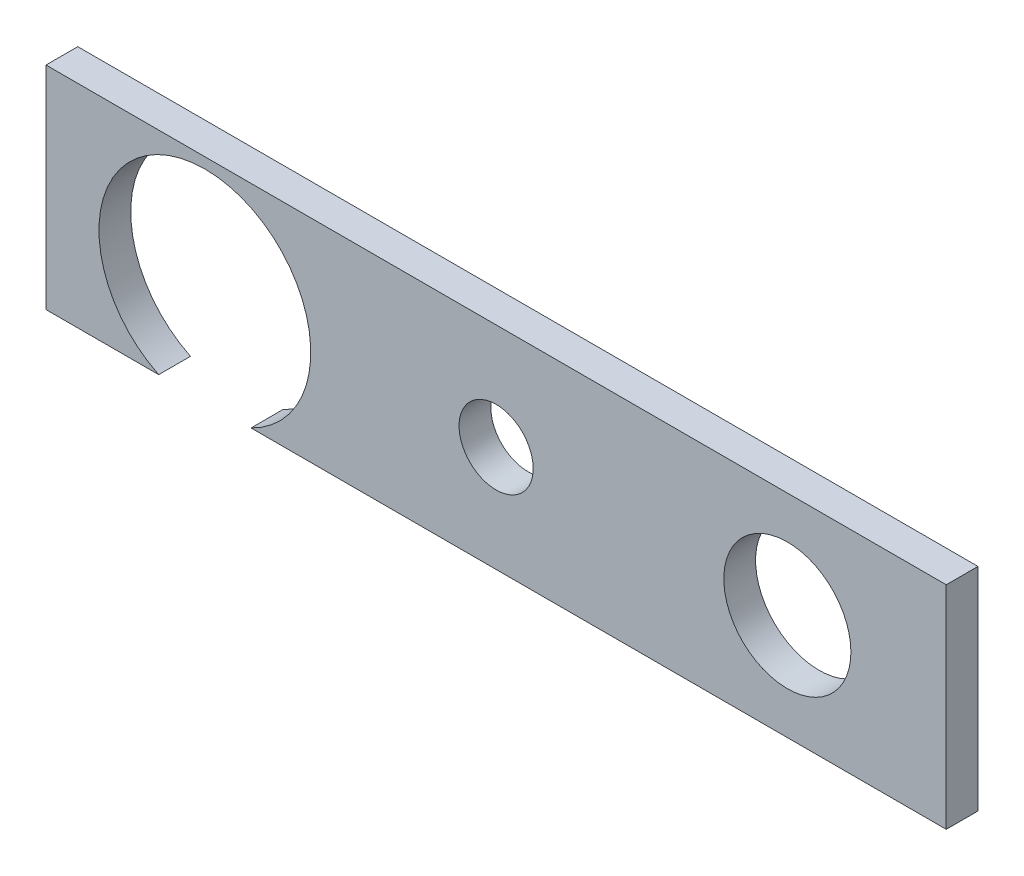
SolidWorks part; units mm, degrees
ref_plane "Front Plane" through (0, 0, 0) normal (0, 0, 1) x (1, 0, 0)
ref_plane "Top Plane" through (0, 0, 0) normal (0, 1, 0) x (1, 0, 0)
ref_plane "Right Plane" through (0, 0, 0) normal (1, 0, 0) x (0, 0, -1)
sketch "Sketch1" plane through (0, 0, 0) normal (0, 0, 1) x (1, 0, 0)
  line L1 (0, 0) -> (85, 0)
  line L2 (0, 0) -> (0, 20)
  line L3 (0, 20) -> (85, 20)
  line L4 (85, 0) -> (85, 20)
  dimension "D1" = 20
  dimension "D2" = 85
extrude "Boss-Extrude1" add sketch "Sketch1" along normal blind 3 contours L3 L4 L1 L2
sketch "Sketch2" plane through (0, 0, 3) normal (0, 0, 1) x (1, 0, 0)
  line L0 (85, 0) -> (85, 20) construction
  line L1 (0, 0) -> (85, 0) construction
  circle A0 centre (42.5, 10) radius 3.5
  circle A1 centre (70, 10) radius 6
  circle A2 centre (15, 9) radius 10
  point P9 (85, 10)
  dimension "D1" = 20
  dimension "D2" = 7
  dimension "D3" = 12
  dimension "D4" = 15
  dimension "D5" = 70
  dimension "D6" = 42.5
  dimension "D7" = 9
extrude "Cut-Extrude1" cut sketch "Sketch2" against normal through all
